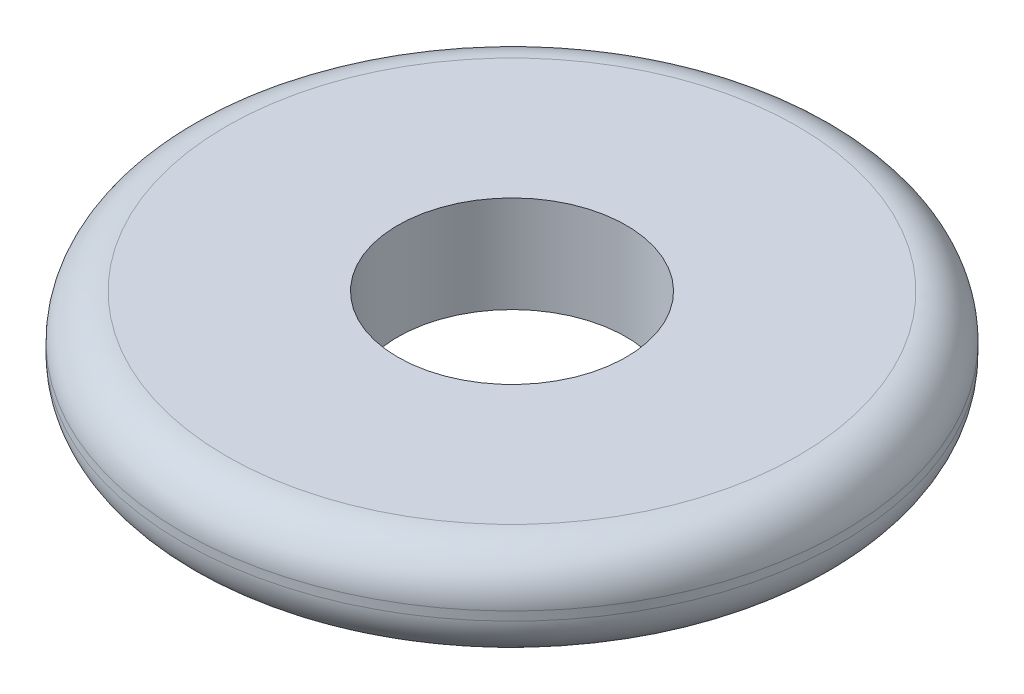
SolidWorks part; units mm, degrees
material "POLYURETHANE (11671)"
ref_plane "Front" through (0, 0, 0) normal (0, 0, 1) x (1, 0, 0)
ref_plane "Top" through (0, 0, 0) normal (0, 1, 0) x (1, 0, 0)
ref_plane "Right" through (0, 0, 0) normal (1, 0, 0) x (0, 0, -1)
sketch "Sketch1" plane through (0, 0, 0) normal (0, 1, 0) x (1, 0, 0)
  circle A0 centre (0, 0) radius 3.75
  dimension "D1" = 7.5
extrude "Boss-Extrude1" add sketch "Sketch1" along normal blind 1.1
sketch "Sketch2" plane through (0, 1.1, 0) normal (0, 1, 0) x (1, 0, 0)
  circle A0 centre (0, 0) radius 1.3
  dimension "D1" = 2.6
extrude "Cut-Extrude1" cut sketch "Sketch2" against normal through all
fillet "Fillet1" radius 0.5 2 edges at (0, 0, 3.75) (0, 1.1, 3.75)
